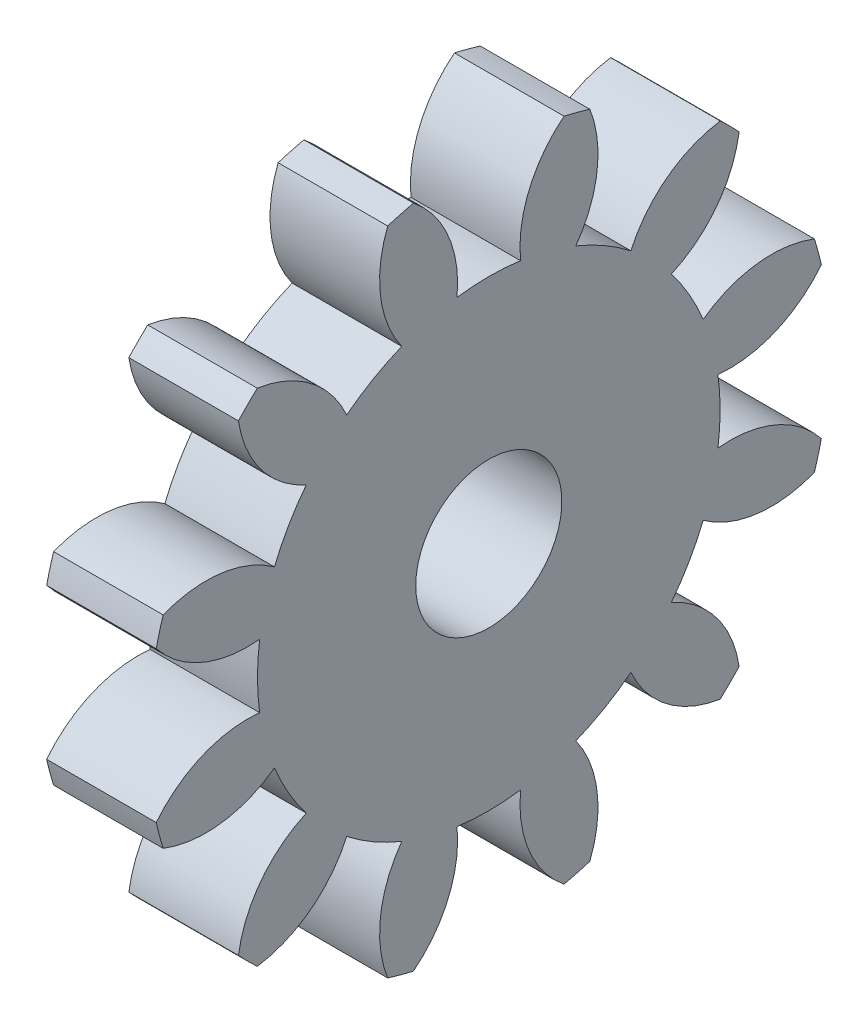
SolidWorks part; units mm, degrees
material "PVC 0.007 Plasticized"
ref_plane "Plane1" through (0, 0, 0) normal (0, 0, 1) x (1, 0, 0)
ref_plane "Plane2" through (0, 0, 0) normal (0, 1, 0) x (1, 0, 0)
ref_plane "Plane3" through (0, 0, 0) normal (1, 0, 0) x (0, 0, -1)
other "Configuration Table"
sketch "HoldingSke" plane through (0, 0, 0) normal (0, 1, 0) x (1, 0, 0)
  line L0 (0, 0) -> (298.1394, -63.3715)
  line L1 (-15, 0) -> (100, 0) construction
  line L2 (0, 0) -> (-2.1039, 2.3779)
  line L3 (0, 0) -> (-11.863, 4.5341)
  line L4 (0, 0) -> (8.4473, 1.7955)
  line L5 (0, 0) -> (-47.5972, -17.7524)
  line L6 (0, 0) -> (-3.9479, -2.6637)
  line L7 (-2.1039, 2.3779) -> (8.8308, 51.9871)
  line L8 (-76.2, 54.61) -> (-69.596, 54.61)
  line L9 (-67.7845, 28.3722) -> (-49.3413, 33.142)
  line L10 (-76.2, 71.12) -> (104.1128, 71.12)
  line L11 (0, 0) -> (-4.7625, 0)
  line L12 (-76.2, 101.6) -> (-76.1147, 101.6)
  line L13 (24.9733, 27.94) -> (52.9518, 28.4284)
  line L14 (24.9733, 27.94) -> (24.9746, 27.94)
  line L15 (24.9733, 27.94) -> (100.4006, 29.5858)
  circle A0 centre (0, 0) radius 3.175
  circle A1 centre (0, 0) radius 10.0529
  circle A2 centre (0, 0) radius 38.1
  circle A3 centre (0, 0) radius 3.175
  dimension "MHD" = 20.1058
  dimension "Hub_dia" = 76.2
  dimension "Bore" = 6.35
  dimension "MBD" = 6.35
  dimension "Num_teeth" = 12
  dimension "Pitch" = 304.8
  dimension "Overall_len" = 50.8
  dimension "Show_teeth" = 12
  dimension "Thickness" = 4.7625
  dimension "OAL" = 50.8001
  dimension "T_dim" = 6.604
  dimension "Ap" = 14.5
  dimension "H" = 19.05
  dimension "Pitch_radius" = 180.3128
  dimension "Width" = 4.7625
  dimension "Backlash" = 0.0853
  dimension "Addendum_fac" = 1
  dimension "Dedendum_fac" = 1.25
  dimension "Clearance_fac" = 0.25
  dimension "Dedendum_add" = 0.0013
sketch "BasProSke" plane through (0, 0, 0) normal (0, 1, 0) x (1, 0, 0)
  line L0 (-10, 0) -> (60, 0) construction
  line L1 (0, 0) -> (0, 14.8167)
  line L2 (0, 0) -> (4.7625, 0)
  line L3 (4.7625, 0) -> (4.7625, 14.8167)
  line L4 (4.7625, 14.8167) -> (0, 14.8167)
  dimension "Thickness" = 4.7625
  dimension "Diameter" = 29.6333
revolve "Base-Revolve" add sketch "BasProSke" angle 360 about L0
sketch "TooCutSke" plane through (0, 0, 0) normal (1, 0, 0) x (0, 0, -1)
  line L1 (0, 0) -> (0, 107) construction
  line L2 (0, 0) -> (-1.8068, 12.5708) construction
  line L3 (0, 0) -> (-6.5275, 24.3609) construction
  line L4 (-1.8068, 12.5708) -> (-3.2637, 12.1804) construction
  arc A0 (1.3818, 9.9575) -> (-1.3818, 9.9575) centre (0, 0) ccw
  arc A1 (3.2965, 14.4713) -> (-3.2965, 14.4713) centre (0, 0) ccw
  circle A2 centre (0, 0) radius 12.7 construction
  circle A3 centre (0, 0) radius 12.2955 construction
  arc A4 (-1.3818, 9.9575) -> (-3.2965, 14.4713) centre (-6.4352, 10.477) ccw
  arc A5 (3.2965, 14.4713) -> (1.3818, 9.9575) centre (6.4352, 10.477) ccw
  dimension "Root_dia" = 20.1058
  dimension "Overcut_dia" = 29.6841
  dimension "Pitch_dia" = 25.4
  dimension "Base_dia" = 24.591
  dimension "Flank_rad" = 5.08
  dimension "Half_ang" = 15
  dimension "Half_CT" = 1.5083
extrude "ToothCut" cut sketch "TooCutSke" along normal through all
fillet "Breaks" [suppressed] radius 0.0423
fillet "RootFillets" [suppressed] radius 0.5304
pattern_circular "TeethCuts" count 12 every 30 about axis through (-10, 0, 0) along (1, 0, 0) of "ToothCut", "RootFillets", "Breaks"
sketch "HubNeaOneSke" plane through (0, 0, 0) normal (-1, 0, 0) x (0, 0, 1)
  circle A0 centre (0, 0) radius 10.0529
  dimension "Diameter" = 20.1058
extrude "HubNearOne" [suppressed] add sketch "HubNeaOneSke" along normal blind 46.0376
sketch "HubNeaBotSke" plane through (0, 0, 0) normal (-1, 0, 0) x (0, 0, 1)
  circle A0 centre (0, 0) radius 10.0529
  dimension "Diameter" = 20.1058
extrude "HubNearBoth" [suppressed] add sketch "HubNeaBotSke" along normal blind 23.0188
ref_plane "FarPln" through (4.7625, 0, 0) normal (1, 0, 0) x (0, 0, -1)
sketch "HubFarSke" plane through (4.7625, 0, 0) normal (1, 0, 0) x (0, 0, -1)
  circle A0 centre (0, 0) radius 10.0529
  dimension "Diameter" = 20.1058
extrude "HubFar" [suppressed] add sketch "HubFarSke" along normal blind 23.0188
sketch "BorSke" plane through (0, 0, 0) normal (1, 0, 0) x (0, 0, -1)
  circle A0 centre (0, 0) radius 3.175
  dimension "Diameter" = 6.35
extrude "Bore" cut sketch "BorSke" along normal mid plane 101.6001
sketch "KeySke" plane through (0, 0, 0) normal (1, 0, 0) x (0, 0, -1)
  line L0 (-0.127, 0) -> (-0.127, 3.429)
  line L1 (-0.127, 3.429) -> (0.127, 3.429)
  line L2 (0.127, 3.429) -> (0.127, 0)
  line L3 (0, 0) -> (0, 34) construction
  line L4 (-0.127, 0) -> (0.127, 0)
  dimension "Offset" = 3.429
  dimension "Width" = 0.254
extrude "Keyway" [suppressed] cut sketch "KeySke" along normal mid plane 101.6001
pattern_circular "Keyway2" [suppressed] count 2 every 90 about axis through (-10, 0, 0) along (1, 0, 0)
equation "' \"Pitch@HoldingSke\" = 4"
equation "' \"Num_teeth@HoldingSke\" = 12"
equation "' \"Ap@HoldingSke\" =  20"
equation "' \"Ap@HoldingSke\" = 20"
equation "' \"Width@HoldingSke\" = 0.5"
equation "' \"Hub_dia@HoldingSke\"= 1"
equation "' \"Hub_dia@HoldingSke\" = 1"
equation "' \"Overall_len@HoldingSke\" = 1.0"
equation "' \"Bore@HoldingSke\" = 0.75"
equation "' \"T_dim@HoldingSke\" = 0.85"
equation "' \"Width@KeySke\" = 0.25"
equation "' \"Show_teeth@HoldingSke\" = 13"
equation "' \"Backlash@HoldingSke\" = 0.009"
equation "' \"Addendum_fac@HoldingSke\" = 1.0"
equation "' \"Dedendum_fac@HoldingSke\" = 1.25"
equation "' \"Dedendum_add@HoldingSke\" = 0.00005"
equation "' \"Clearance_fac@HoldingSke\" = 0.25"
equation "' \"Pitch@HoldingSke\" = 0.5"
equation "' \"Num_teeth@HoldingSke\" = 23"
equation "' \"Show_teeth@HoldingSke\" = 23"
equation "' \"Backlash@HoldingSke\" = 0.0375"
equation "\"Overcut_dia@TooCutSke\" = (\"Num_teeth@HoldingSke\" + 2 * \"Addendum_fac@HoldingSke\") / \"Pitch@HoldingSke\" + 0.002"
equation "\"Pitch_dia@TooCutSke\" = \"Num_teeth@HoldingSke\" / \"Pitch@HoldingSke\""
equation "\"Base_dia@TooCutSke\" = \"Num_teeth@HoldingSke\" / \"Pitch@HoldingSke\" * cos((\"Ap@HoldingSke\"  * 3.14159265 / 180))"
equation "\"Root_dia@TooCutSke\" = (\"Num_teeth@HoldingSke\" + 2) / \"Pitch@HoldingSke\" - 2 * (\"Addendum_fac@HoldingSke\" + \"Dedendum_fac@HoldingSke\") / \"Pitch@HoldingSke\" - \"Dedendum_add@HoldingSke\" * 2"
equation "\"Half_ang@TooCutSke\" = 180 / \"Num_teeth@HoldingSke\""
equation "\"Half_CT@TooCutSke\" = \"Num_teeth@HoldingSke\" / \"Pitch@HoldingSke\" * sin((3.14159265 / 2 / \"Num_teeth@HoldingSke\")) / 2 - 7 * \"Backlash@HoldingSke\" / 4"
equation "\"Flank_rad@TooCutSke\" = \"Num_teeth@HoldingSke\" / \"Pitch@HoldingSke\" / 5"
equation "\"Radius@RootFillets\" = \"Clearance_fac@HoldingSke\" / \"Pitch@HoldingSke\" + \"Dedendum_add@HoldingSke\""
equation "\"Break_rad@Breaks\" = 0.02 / \"Pitch@HoldingSke\""
equation "\"Thickness@HoldingSke\" = \"Width@HoldingSke\""
equation "\"OAL@HoldingSke\" = \"Thickness@HoldingSke\""
equation "\"MHD@HoldingSke\" = (\"Num_teeth@HoldingSke\" + 2) / \"Pitch@HoldingSke\" - 2 * (\"Addendum_fac@HoldingSke\" + \"Dedendum_fac@HoldingSke\")  / \"Pitch@HoldingSke\" - \"Dedendum_add@HoldingSke\" * 2"
equation "\"MBD@HoldingSke\" = (\"Num_teeth@HoldingSke\" + 2) / \"Pitch@HoldingSke\" - 2 * (\"Addendum_fac@HoldingSke\" + \"Dedendum_fac@HoldingSke\")  / \"Pitch@HoldingSke\" - \"Dedendum_add@HoldingSke\" * 2 - 0.002"
equation "\"MHD@HoldingSke\" = ((sgn( \"MHD@HoldingSke\" - \"Hub_dia@HoldingSke\" )-1)*( \"MHD@HoldingSke\" - \"Hub_dia@HoldingSke\" ))/-2+ \"Hub_dia@HoldingSke\""
equation "\"MBD@HoldingSke\" = ((sgn( \"MBD@HoldingSke\" - \"Bore@HoldingSke\" )-1)*( \"MBD@HoldingSke\" - \"Bore@HoldingSke\" ))/-2+ \"Bore@HoldingSke\""
equation "\"OAL@HoldingSke\" = ((sgn( \"OAL@HoldingSke\" - \"Overall_len@HoldingSke\" )+1)*( \"OAL@HoldingSke\" - \"Overall_len@HoldingSke\" ))/2 + \"Overall_len@HoldingSke\" + 0.000002"
equation "\"Num_teeth@TeethCuts\" = int( \"Show_teeth@HoldingSke\" ) + 1"
equation "\"Num_teeth@TeethCuts\" = ((sgn( \"Num_teeth@TeethCuts\" - \"Num_teeth@HoldingSke\" )-1)*( \"Num_teeth@TeethCuts\" - \"Num_teeth@HoldingSke\" ))/-2+ \"Num_teeth@HoldingSke\""
equation "\"Num_teeth@TeethCuts\" = ((sgn( \"Num_teeth@TeethCuts\" - 2.0)+1)*( \"Num_teeth@TeethCuts\" - 2.0))/2 +2.0"
equation "\"Angle@TeethCuts\" = 360.0 / \"Num_teeth@HoldingSke\""
equation "\"Diameter@BasProSke\" = (\"Num_teeth@HoldingSke\" + 2 * \"Addendum_fac@HoldingSke\") / \"Pitch@HoldingSke\""
equation "\"Thickness@BasProSke\"  = \"Thickness@HoldingSke\""
equation "' \"Fillet_rad@BasProSke\" =  \"Thickness@HoldingSke\" * 0.05"
equation "' \"Fillet_rad@BasProSke\" = \"Thickness@HoldingSke\" * 0.05"
equation "\"MHD@HoldingSke\" = ((sgn( \"MHD@HoldingSke\" - \"Root_dia@TooCutSke\" )-1)*( \"MHD@HoldingSke\" - \"Root_dia@TooCutSke\" ))/-2+ \"Root_dia@TooCutSke\""
equation "\"Diameter@HubNeaOneSke\" = \"MHD@HoldingSke\""
equation "\"Length@HubNearOne\" = \"OAL@HoldingSke\" - \"Thickness@BasProSke\""
equation "\"Diameter@HubNeaBotSke\" = \"MHD@HoldingSke\""
equation "\"Length@HubNearBoth\" = ( \"OAL@HoldingSke\" - \"Thickness@BasProSke\" ) / 2.0"
equation "\"Thickness@FarPln\" = \"Thickness@BasProSke\""
equation "\"Diameter@HubFarSke\" = \"MHD@HoldingSke\""
equation "\"Length@HubFar\" = ( \"OAL@HoldingSke\" - \"Thickness@BasProSke\" ) / 2.0"
equation "\"Diameter@BorSke\" = \"MBD@HoldingSke\""
equation "\"D1@Bore\" = \"OAL@HoldingSke\" * 2.0"
equation "\"D1@Keyway\" = \"OAL@HoldingSke\" * 2.0"
equation "\"Offset@KeySke\" = \"T_dim@HoldingSke\" - \"MBD@HoldingSke\" / 2.0"
